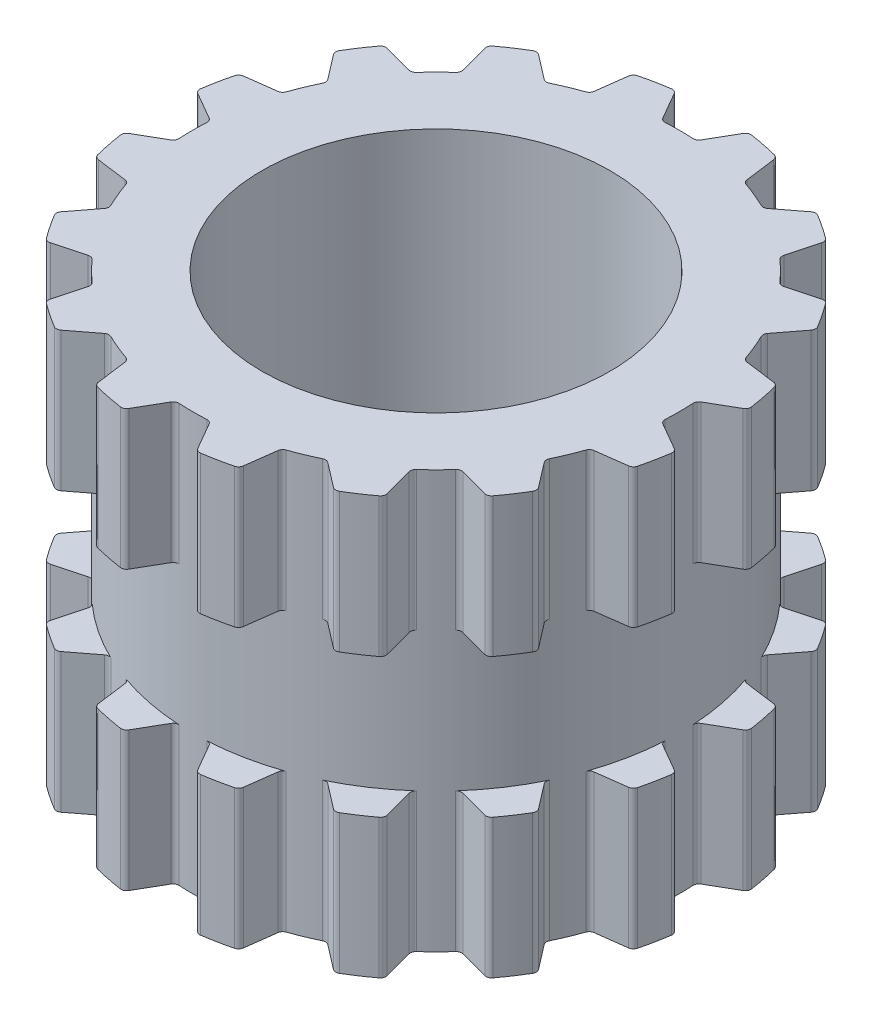
SolidWorks part; units mm, degrees
material "Brass"
ref_plane "Front Plane" through (0, 0, 0) normal (0, 0, 1) x (1, 0, 0)
ref_plane "Top Plane" through (0, 0, 0) normal (0, 1, 0) x (1, 0, 0)
ref_plane "Right Plane" through (0, 0, 0) normal (1, 0, 0) x (0, 0, -1)
ref_axis "CentralAxis" through (0, 5.5, 0) along (0, -1, 0)
sketch "BodyS" plane through (0, 0, 0) normal (0, 0, 1) x (1, 0, 0)
  line L0 (0, 1.5) -> (2, 1.5)
  line L1 (2, 1.5) -> (2, -1.5)
  line L6 (2, -1.5) -> (0, -1.5)
  line L7 (0, -1.5) -> (0, 1.5) construction
  dimension "Height" = 3
  dimension "ThreadInsertDiameter" = 4
revolve "Body" add sketch "BodyS" angle 360 about L7
hole_wizard "M3x0.5 Tapped Hole1" positions "Sketch2" profile "Sketch3" tap size "M3x0.5" standard "ANSI Metric" end condition through all
sketch "Sketch2" plane through (0, 1.5, 0) normal (0, 1, 0) x (1, 0, 0)
  point P0 (0, 0)
sketch "Sketch3" plane through (0, 1.5, 0) normal (1, 0, 0) x (0, 0, 1)
  line L0 (0, 0) -> (0, 3)
  line L1 (0, 3) -> (1.25, 3)
  line L2 (1.25, 3) -> (1.25, 0)
  line L5 (1.25, 0) -> (0, 0)
  line L11 (0, -6.35) -> (0, 107.95) construction
  dimension "Thru Tap Drill Dia." = 2.5
  dimension "Thru Tap Drill Depth" = 3
cosmetic thread "Hole Thread1" parameters "D2"=3
sketch "MidBodyCutS" plane through (0, 0, 0) normal (0, 0, 1) x (1, 0, 0)
  line L1 (2, 0.5) -> (1.75, 0.5)
  line L2 (2, 0.5) -> (2, -0.5)
  line L3 (2, -0.5) -> (1.75, -0.5)
  line L4 (1.75, 0.5) -> (1.75, -0.5)
  line L5 (2, 0.5) -> (1.75, -0.5) construction
  line L6 (2, -0.5) -> (1.75, 0.5) construction
  line L7 (2, -1.5) -> (2, 1.5) construction
  line L8 (0, 0) -> (1.875, 0) construction
  line L9 (2, 1.5) -> (-2, 1.5) construction
  point P0 (1.875, 0)
  dimension "Width" = 0.25
  dimension "RefHeight" = 1
  dimension "Height" = 1
revolve "MidBodyCut" cut sketch "MidBodyCutS" angle 360 about axis through (0, 5.5, 0) along (0, -1, 0)
sketch "GrooveCutS" plane through (0, 0, 0) normal (0, 1, 0) x (1, 0, 0)
  line L4 (0, 0) -> (0, 1.75) construction
  line L5 (0.1369, 1.7671) -> (0.248, 1.9595)
  line L6 (0, 1.75) -> (0, 2) construction
  line L7 (-0.1369, 1.7671) -> (-0.248, 1.9595)
  circle A0 centre (0, 0) radius 1.75 construction
  circle A1 centre (0, 0) radius 2 construction
  arc A2 (0.0999, 1.7471) -> (-0.0999, 1.7471) centre (0, 0) ccw
  arc A3 (0.2884, 1.9791) -> (-0.2884, 1.9791) centre (0, 0) ccw
  arc A4 (0.248, 1.9595) -> (0.2884, 1.9791) centre (0.2826, 1.9395) cw
  arc A5 (0.1369, 1.7671) -> (0.0999, 1.7471) centre (0.1022, 1.7871) cw
  arc A6 (-0.248, 1.9595) -> (-0.2884, 1.9791) centre (-0.2826, 1.9395) ccw
  arc A7 (-0.1369, 1.7671) -> (-0.0999, 1.7471) centre (-0.1022, 1.7871) ccw
  point P14 (0.1245, 1.7456)
  dimension "RefInnerDiameter" = 3.5
  dimension "InnerRadius" = 0.04
  dimension "OuterRadius" = 0.04
  dimension "Depth" = 0.25
  dimension "Angle" = 60
  dimension "RefOuterWidth" = 0.5768
  dimension "InnerArcWidth" = 0.2
extrude "GrooveCut" cut sketch "GrooveCutS" against normal through all both and the other way through all
pattern_circular "GCCP" count 16 over 360 about axis through (0, 0, 0) along (0, 1, 0) of "GrooveCut"
